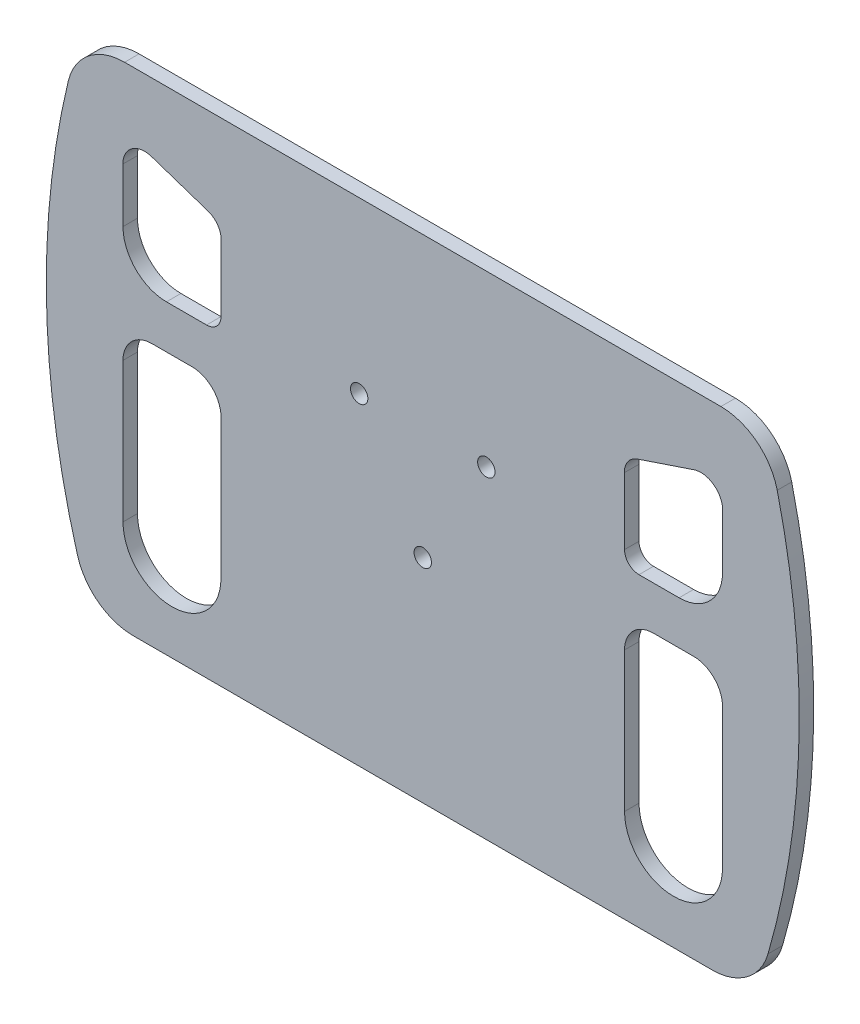
SolidWorks part; units mm, degrees
material "Hexcel AS4C (3000 Filamentów)"
ref_plane "Płaszczyzna przednia" through (0, 0, 0) normal (0, 0, 1) x (1, 0, 0)
ref_plane "Płaszczyzna górna" through (0, 0, 0) normal (0, 1, 0) x (1, 0, 0)
ref_plane "Płaszczyzna prawa" through (0, 0, 0) normal (1, 0, 0) x (0, 0, -1)
sketch "Szkic1" plane through (0, 0, 0) normal (0, 0, 1) x (1, 0, 0)
  line L0 (-103.5576, 139.2503) -> (-103.5033, 120.578)
  line L2 (0, 0) -> (-100, 0)
  line L3 (0, 0) -> (0, 170)
  line L4 (0, 170) -> (-102.948, 170)
  line L8 (-93.5033, 90.578) -> (-79.6715, 90.578)
  line L9 (-103.5033, 80.578) -> (-103.5033, 32.2627)
  line L11 (-69.6715, 80.578) -> (-69.6715, 32.2627)
  line L12 (-93.6368, 146.4304) -> (-74.1441, 139.8919)
  line L13 (-69.6571, 110.5636) -> (-69.5907, 133.5231)
  line L14 (-88.5033, 105.578) -> (-74.6571, 105.578)
  arc A0 (-129.0614, 113.105) -> (-119.2145, 14.45) centre (144.3353, 90.5743) ccw
  arc A1 (-122.3944, 154.6732) -> (-119.2145, 14.45) centre (144.3353, 90.5743) ccw
  arc A2 (-100, 0) -> (-119.2145, 14.45) centre (-100, 20) cw
  arc A3 (-122.3944, 154.6732) -> (-102.948, 170) centre (-102.948, 150) cw
  arc A4 (-88.5033, 105.578) -> (-103.5033, 120.578) centre (-88.5033, 120.578) cw
  arc A5 (-93.6368, 146.4304) -> (-103.5576, 139.2503) centre (-96.0305, 139.294) ccw
  arc A6 (-69.5907, 133.5231) -> (-74.1441, 139.8919) centre (-76.2674, 133.5618) ccw
  arc A7 (-69.6571, 110.5636) -> (-74.6571, 105.578) centre (-74.6571, 110.578) cw
  arc A8 (-103.5033, 32.2627) -> (-69.6715, 32.2627) centre (-86.5874, 32.2627) ccw
  arc A9 (-69.6715, 80.578) -> (-79.6715, 90.578) centre (-79.6715, 80.578) ccw
  arc A10 (-93.5033, 90.578) -> (-103.5033, 80.578) centre (-93.5033, 80.578) ccw
  dimension "D1" = 20
  dimension "D2" = 15
  dimension "D3" = 5
  dimension "D5" = 10
  dimension "D4" = 100
extrude "Dodanie-wyciągnięcie1" add sketch "Szkic1" along normal blind 5 contours A3 A1 A0 A2 L2 L3 L4 A10 L8 A9 L11 A8 L9 L13 A7 L14 A4 L0 A5 L12 A6
mirror "Lustro1" about plane through (0, 0, 5) normal (-1, 0, 0) of "Dodanie-wyciągnięcie1"
sketch "Szkic3" plane through (0, 0, 5) normal (0, 0, 1) x (1, 0, 0)
  line L4 (-93.5033, 90.578) -> (-79.6715, 90.578) construction
  line L5 (-129.8667, 90.578) -> (-129.8667, 98.7386)
  arc A1 (-122.3944, 154.6732) -> (-119.2145, 14.45) centre (144.3353, 90.5743) ccw construction
  circle A2 centre (0, 73.3886) radius 3
  circle A3 centre (-21.955, 111.4158) radius 3
  circle A5 centre (21.955, 111.4158) radius 3
  dimension "D2" = 43.91
  dimension "D5" = 111.4158
  dimension "D3" = 43.91
  dimension "D7" = 6
  dimension "D8" = 6
  dimension "D9" = 6
  dimension "D11" = 73.3886
  dimension "D1" = 21.955
  dimension "D4" = 43.91
  dimension "D6" = 111.4158
  dimension "D10" = 21.955
extrude "Wytnij-wyciągnięcie1" cut sketch "Szkic3" against normal blind 5 contours A3 | A5 | A2
